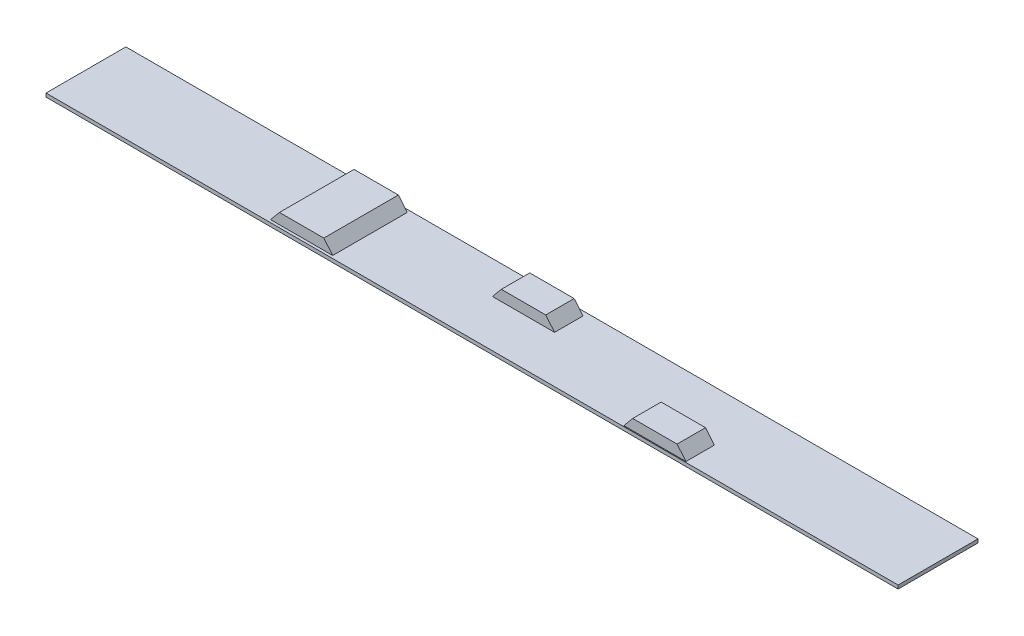
SolidWorks part; units mm, degrees
ref_plane "Front Plane" through (0, 0, 0) normal (0, 0, 1) x (1, 0, 0)
ref_plane "Top Plane" through (0, 0, 0) normal (0, 1, 0) x (1, 0, 0)
ref_plane "Right Plane" through (0, 0, 0) normal (1, 0, 0) x (0, 0, -1)
sketch "Sketch1" plane through (0, 0, 0) normal (0, 1, 0) x (1, 0, 0)
  line L1 (-1200, 112.5) -> (1200, 112.5)
  line L2 (-1200, 112.5) -> (-1200, -112.5)
  line L3 (-1200, -112.5) -> (1200, -112.5)
  line L4 (1200, 112.5) -> (1200, -112.5)
  line L5 (-1200, 112.5) -> (1200, -112.5) construction
  line L6 (-1200, -112.5) -> (1200, 112.5) construction
  point P0 (0, 0)
  dimension "D1" = 2400
  dimension "D2" = 225
extrude "Boss-Extrude1" add sketch "Sketch1" along normal blind 10
sketch "Sketch2" plane through (0, 0, 0) normal (0, 0, 1) x (1, 0, 0)
  line L0 (425, 10) -> (450, 40)
  line L1 (-1200, 10) -> (1200, 10) construction
  line L2 (450, 40) -> (575, 40)
  line L3 (575, 40) -> (600, 10)
  line L4 (600, 10) -> (425, 10)
  line L5 (1200, 10) -> (1200, 0) construction
  point P4 (880.5338, 51.8547)
  point P9 (1200, 5)
  point P10 (485.9758, 40)
  point P11 (579.7221, 40)
  dimension "D1" = 175
  dimension "D2" = 30
  dimension "D3" = 600
  dimension "D4" = 125
extrude "Boss-Extrude2" add sketch "Sketch2" along normal blind 80 from offset 30
sketch "Sketch3" plane through (0, 0, 0) normal (0, 0, 1) x (1, 0, 0)
  line L0 (425, 10) -> (450, 40) construction
  line L1 (600, 10) -> (425, 10) construction
  line L2 (575, 40) -> (600, 10) construction
  line L3 (450, 40) -> (575, 40) construction
  line L4 (425, 10) -> (450, 40) construction
  line L5 (600, 10) -> (425, 10) construction
  line L6 (575, 40) -> (600, 10) construction
  line L7 (450, 40) -> (575, 40) construction
  line L8 (100, 10) -> (-75, 10)
  line L9 (75, 40) -> (100, 10)
  line L10 (-50, 40) -> (75, 40)
  line L11 (-75, 10) -> (-50, 40)
  dimension "D1" = 2
extrude "Boss-Extrude3" add sketch "Sketch3" against normal blind 80 from offset 20 offset against normal yes
sketch "Sketch4" plane through (0, 0, 0) normal (0, 0, 1) x (1, 0, 0)
  line L0 (425, 10) -> (450, 40) construction
  line L1 (600, 10) -> (425, 10) construction
  line L2 (575, 40) -> (600, 10) construction
  line L3 (450, 40) -> (575, 40) construction
  line L4 (425, 10) -> (450, 40) construction
  line L5 (600, 10) -> (425, 10) construction
  line L6 (575, 40) -> (600, 10) construction
  line L7 (450, 40) -> (575, 40) construction
  line L8 (-400, 10) -> (-575, 10)
  line L9 (-550, 40) -> (-425, 40)
  line L10 (-425, 40) -> (-400, 10)
  line L11 (-575, 10) -> (-550, 40)
  dimension "D1" = 2
extrude "Boss-Extrude4" add sketch "Sketch4" along normal mid plane 210
